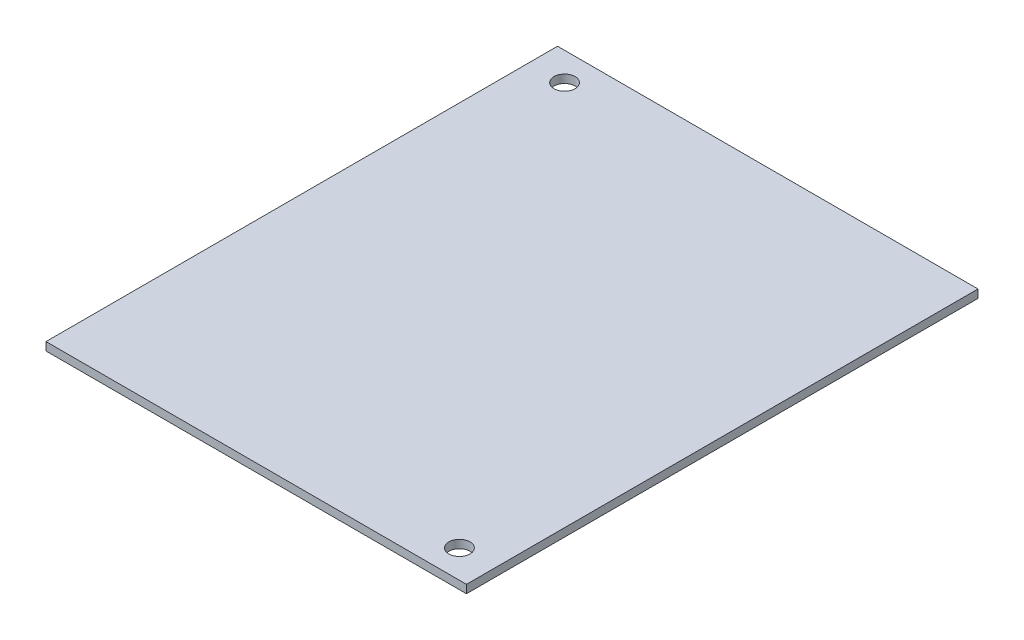
SolidWorks part; units mm, degrees
material "Custom FR4"
ref_plane "Front Plane" through (0, 0, 0) normal (0, 0, 1) x (1, 0, 0)
ref_plane "Top Plane" through (0, 0, 0) normal (0, 1, 0) x (1, 0, 0)
ref_plane "Right Plane" through (0, 0, 0) normal (1, 0, 0) x (0, 0, -1)
sketch "Sketch1" plane through (0, 0, 0) normal (0, 1, 0) x (1, 0, 0)
  line L0 (-30, 36.5) -> (30, -36.5) construction
  line L1 (-30, 36.5) -> (30, 36.5)
  line L2 (-30, 36.5) -> (-30, -36.5)
  line L3 (-30, -36.5) -> (30, -36.5)
  line L4 (30, 36.5) -> (30, -36.5)
  circle A0 centre (25, -32.5) radius 1.5025
  circle A1 centre (-25, 32.5) radius 1.5025
  dimension "D3" = 3.005
  dimension "D4" = 5
  dimension "D5" = 4
  dimension "D6" = 5
  dimension "D7" = 4
  dimension "D1" = 73
  dimension "D2" = 60
extrude "Boss-Extrude1" add sketch "Sketch1" along normal blind 1.17
